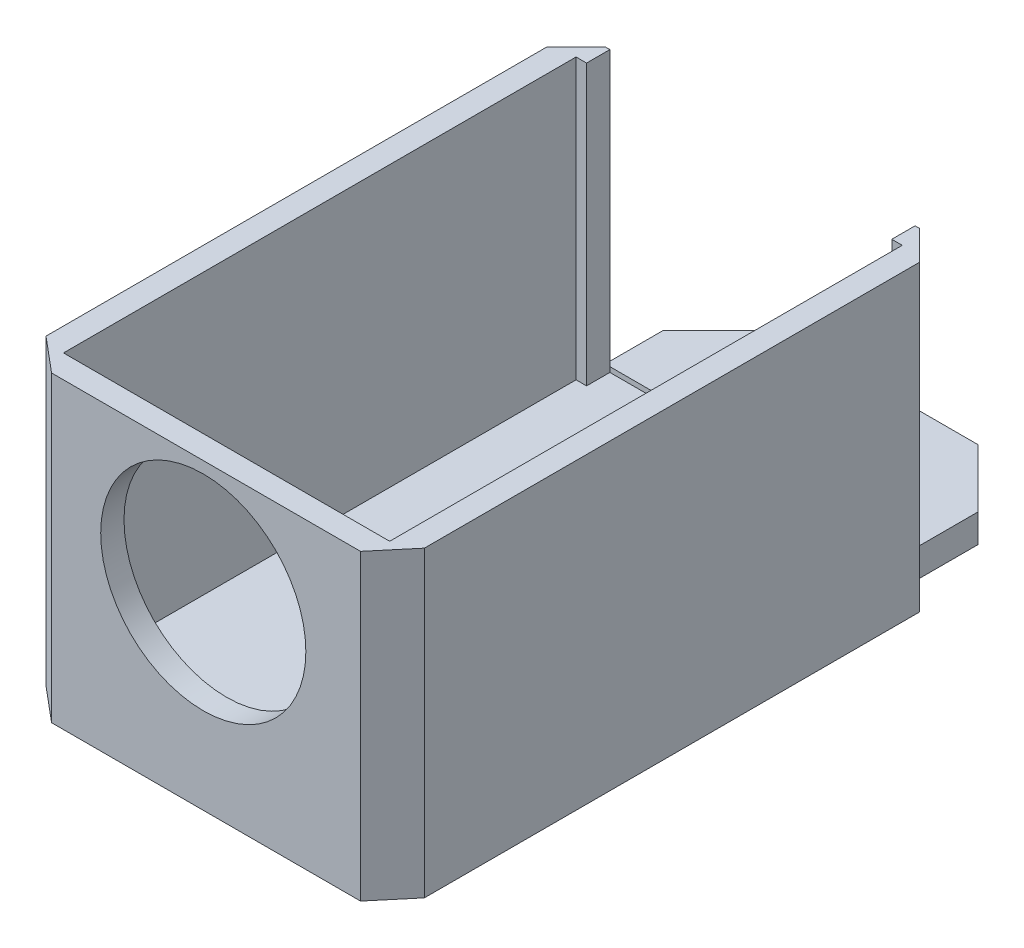
SolidWorks part; units mm, degrees
ref_plane "Front Plane" through (0, 0, 0) normal (0, 0, 1) x (1, 0, 0)
ref_plane "Top Plane" through (0, 0, 0) normal (0, 1, 0) x (1, 0, 0)
ref_plane "Right Plane" through (0, 0, 0) normal (1, 0, 0) x (0, 0, -1)
sketch "Sketch1" plane through (0, 0, 0) normal (0, 1, 0) x (1, 0, 0)
  line L1 (-16, 24) -> (16, 24)
  line L2 (-16, 24) -> (-16, -24)
  line L3 (-16, -24) -> (16, -24)
  line L4 (16, 24) -> (16, -24)
  line L5 (-16, 24) -> (16, -24) construction
  line L6 (-16, -24) -> (16, 24) construction
  point P0 (0, 0)
  dimension "D1" = 32
  dimension "D2" = 48
extrude "Boss-Extrude1" add sketch "Sketch1" along normal blind 26
shell "Shell1" thickness 2
sketch "Sketch2" plane through (0, 0, -24) normal (0, 0, -1) x (-1, 0, 0)
  line L0 (-16, 0) -> (16, 0) construction
  line L1 (-13.1, 2) -> (13.1, 2)
  line L2 (-13.1, 2) -> (-13.1, 26)
  line L3 (-13.1, 26) -> (13.1, 26)
  line L4 (13.1, 2) -> (13.1, 26)
  line L5 (-13.1, 2) -> (13.1, 26) construction
  line L6 (-13.1, 26) -> (13.1, 2) construction
  line L7 (-16, 26) -> (16, 26) construction
  line L8 (16, 26) -> (16, 0) construction
  point P0 (0, 14)
  dimension "D1" = 2
  dimension "D2" = 2.9
extrude "Cut-Extrude1" cut sketch "Sketch2" against normal blind 20
sketch "Sketch3" plane through (0, 0, 24) normal (0, 0, 1) x (1, 0, 0)
  line L0 (-6.8, 26) -> (-5, 18)
  line L1 (-16, 26) -> (16, 26) construction
  line L2 (-5, 18) -> (5, 18)
  line L3 (5, 18) -> (6.8, 26)
  line L4 (0, 18) -> (0, 0) construction
  line L5 (-6.8, 26) -> (6.8, 26)
  point P4 (0, 18)
  dimension "D1" = 10
  dimension "D2" = 8
  dimension "D3" = 1.8
extrude "Cut-Extrude2" [suppressed] cut sketch "Sketch3" against normal blind 20
chamfer "Chamfer1" distance 2.5 angle 50 2 edges at (16, 13, 24) (-16, 13, 24)
chamfer "Chamfer2" [suppressed] distance 0.5 angle 45
sketch "Sketch4" plane through (0, 2, 0) normal (0, 1, 0) x (1, 0, 0)
  line L1 (-14, 22) -> (14, 22)
  line L2 (-14, 22) -> (-14, -22)
  line L3 (-14, -22) -> (14, -22)
  line L4 (14, 22) -> (14, -22)
  line L5 (-14, 22) -> (14, -22) construction
  line L6 (-14, -22) -> (14, 22) construction
  point P0 (0, 0)
  point P6 (0, 0)
  point P7 (0, 0)
extrude "Boss-Extrude2" [suppressed] add sketch "Sketch4" along normal blind 4
chamfer "Chamfer3" distance 2.5 angle 45 2 edges at (-16, 13, -24) (16, 13, -24)
sketch "Sketch5" plane through (0, 0, -24) normal (0, 0, -1) x (-1, 0, 0)
  line L0 (-13.5, 0) -> (13.5, 0)
  line L1 (13.5, 0) -> (13.5, 2.4324)
  line L3 (13.5, 2.4324) -> (-13.5, 2.4324)
  line L4 (-13.5, 26) -> (-13.5, 0) construction
  line L5 (-13.5, 2.4324) -> (-13.5, 0)
extrude "Boss-Extrude3" add sketch "Sketch5" along normal blind 10
chamfer "Chamfer4" distance 5 angle 45 2 edges at (-13.5, 1.2162, -34) (13.5, 1.2162, -34)
sketch "Sketch6" plane through (0, 0, 24) normal (0, 0, 1) x (1, 0, 0)
  circle A0 centre (0, 16.205) radius 8.805
  point P5 (0, 7.4)
  dimension "D1" = 17.61
  dimension "D3" = 7.4
extrude "Cut-Extrude3" cut sketch "Sketch6" against normal blind 10
